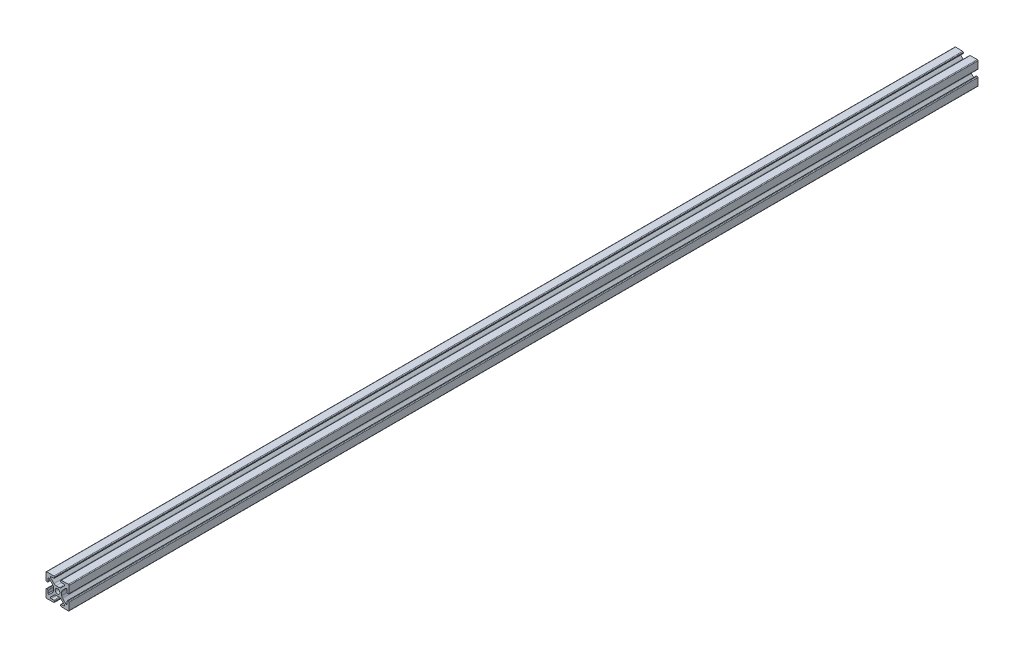
SolidWorks part; units mm, degrees
material "6061 Alloy"
ref_plane "Front Plane" through (0, 0, 0) normal (0, 0, 1) x (1, 0, 0)
ref_plane "Top Plane" through (0, 0, 0) normal (0, 1, 0) x (1, 0, 0)
ref_plane "Right Plane" through (0, 0, 0) normal (1, 0, 0) x (0, 0, -1)
sketch "Sketch1" plane through (0, 0, 0) normal (0, 0, 1) x (-1, 0, 0)
  line L72 (12.7, -11.928) -> (12.5979, -4.1277)
  line L73 (11.836, -3.3757) -> (11.2116, -3.3757)
  line L74 (10.4496, -4.1377) -> (10.4496, -7.0114)
  line L75 (9.1488, -7.5503) -> (5.5122, -3.9136)
  line L76 (4.5822, -1.6588) -> (4.5822, 1.6588)
  line L77 (5.5122, 3.9136) -> (9.1488, 7.5503)
  line L78 (10.4496, 7.0114) -> (10.4496, 4.1377)
  line L79 (11.2116, 3.3757) -> (11.836, 3.3757)
  line L80 (12.5979, 4.1277) -> (12.7, 11.928)
  line L81 (11.928, 12.7) -> (4.1277, 12.5979)
  line L82 (3.3757, 11.836) -> (3.3757, 11.2116)
  line L83 (4.1377, 10.4496) -> (7.0114, 10.4496)
  line L84 (7.5502, 9.1487) -> (3.9135, 5.5121)
  line L85 (1.6587, 4.5822) -> (-1.6686, 4.5822)
  line L86 (-3.9137, 5.5121) -> (-7.5503, 9.1487)
  line L87 (-7.0115, 10.4496) -> (-4.1377, 10.4496)
  line L88 (-3.3757, 11.2116) -> (-3.3757, 11.8359)
  line L89 (-4.1278, 12.5978) -> (-11.9281, 12.6999)
  line L90 (-12.7, 11.928) -> (-12.5979, 4.1277)
  line L91 (-11.836, 3.3757) -> (-11.2116, 3.3757)
  line L92 (-10.4496, 4.1377) -> (-10.4496, 7.0114)
  line L93 (-9.1488, 7.5503) -> (-5.5122, 3.9136)
  line L94 (-4.5822, 1.6588) -> (-4.5822, -1.6588)
  line L95 (-5.5122, -3.9136) -> (-9.1488, -7.5503)
  line L96 (-10.4496, -7.0114) -> (-10.4496, -4.1377)
  line L97 (-11.2116, -3.3757) -> (-11.836, -3.3757)
  line L98 (-12.5979, -4.1277) -> (-12.7, -11.928)
  line L99 (-11.928, -12.7) -> (-4.1277, -12.5979)
  line L100 (-3.3757, -11.836) -> (-3.3757, -11.2116)
  line L101 (-4.1377, -10.4496) -> (-7.0114, -10.4496)
  line L102 (-7.5503, -9.1488) -> (-3.9136, -5.5122)
  line L103 (-1.6685, -4.5822) -> (1.6588, -4.5822)
  line L104 (3.9136, -5.5122) -> (7.5503, -9.1488)
  line L105 (7.0114, -10.4496) -> (4.1377, -10.4496)
  line L106 (3.3757, -11.2116) -> (3.3757, -11.836)
  line L107 (4.1277, -12.5979) -> (11.928, -12.7)
  circle A1 centre (0, 0) radius 2.5527
  arc A72 (11.928, -12.7) -> (12.7, -11.928) centre (11.9381, -11.9381) ccw
  arc A73 (12.5979, -4.1277) -> (11.836, -3.3757) centre (11.836, -4.1377) ccw
  arc A74 (11.2116, -3.3757) -> (10.4496, -4.1377) centre (11.2116, -4.1377) ccw
  arc A75 (9.1488, -7.5503) -> (10.4496, -7.0114) centre (9.6876, -7.0114) ccw
  arc A76 (4.5822, -1.6588) -> (5.5122, -3.9136) centre (7.7809, -1.6588) ccw
  arc A77 (5.5122, 3.9136) -> (4.5822, 1.6588) centre (7.7809, 1.6588) ccw
  arc A78 (10.4496, 7.0114) -> (9.1488, 7.5503) centre (9.6876, 7.0114) ccw
  arc A79 (10.4496, 4.1377) -> (11.2116, 3.3757) centre (11.2116, 4.1377) ccw
  arc A80 (11.836, 3.3757) -> (12.5979, 4.1277) centre (11.836, 4.1377) ccw
  arc A81 (12.7, 11.928) -> (11.928, 12.7) centre (11.9381, 11.9381) ccw
  arc A82 (4.1277, 12.5979) -> (3.3757, 11.836) centre (4.1377, 11.836) ccw
  arc A83 (3.3757, 11.2116) -> (4.1377, 10.4496) centre (4.1377, 11.2116) ccw
  arc A84 (7.5502, 9.1487) -> (7.0114, 10.4496) centre (7.0114, 9.6876) ccw
  arc A85 (1.6587, 4.5822) -> (3.9135, 5.5121) centre (1.6587, 7.7808) ccw
  arc A86 (-3.9137, 5.5121) -> (-1.6686, 4.5822) centre (-1.6686, 7.7572) ccw
  arc A87 (-7.0115, 10.4496) -> (-7.5503, 9.1487) centre (-7.0115, 9.6876) ccw
  arc A88 (-4.1377, 10.4496) -> (-3.3757, 11.2116) centre (-4.1377, 11.2116) ccw
  arc A89 (-3.3757, 11.8359) -> (-4.1278, 12.5978) centre (-4.1377, 11.8359) ccw
  arc A90 (-11.9281, 12.6999) -> (-12.7, 11.928) centre (-11.9381, 11.938) ccw
  arc A91 (-12.5979, 4.1277) -> (-11.836, 3.3757) centre (-11.836, 4.1377) ccw
  arc A92 (-11.2116, 3.3757) -> (-10.4496, 4.1377) centre (-11.2116, 4.1377) ccw
  arc A93 (-9.1488, 7.5503) -> (-10.4496, 7.0114) centre (-9.6876, 7.0114) ccw
  arc A94 (-4.5822, 1.6588) -> (-5.5122, 3.9136) centre (-7.7809, 1.6588) ccw
  arc A95 (-5.5122, -3.9136) -> (-4.5822, -1.6588) centre (-7.7809, -1.6588) ccw
  arc A96 (-10.4496, -7.0114) -> (-9.1488, -7.5503) centre (-9.6876, -7.0114) ccw
  arc A97 (-10.4496, -4.1377) -> (-11.2116, -3.3757) centre (-11.2116, -4.1377) ccw
  arc A98 (-11.836, -3.3757) -> (-12.5979, -4.1277) centre (-11.836, -4.1377) ccw
  arc A99 (-12.7, -11.928) -> (-11.928, -12.7) centre (-11.9381, -11.9381) ccw
  arc A100 (-4.1277, -12.5979) -> (-3.3757, -11.836) centre (-4.1377, -11.836) ccw
  arc A101 (-3.3757, -11.2116) -> (-4.1377, -10.4496) centre (-4.1377, -11.2116) ccw
  arc A102 (-7.5503, -9.1488) -> (-7.0114, -10.4496) centre (-7.0114, -9.6876) ccw
  arc A103 (-1.6685, -4.5822) -> (-3.9136, -5.5122) centre (-1.6685, -7.7572) ccw
  arc A104 (3.9136, -5.5122) -> (1.6588, -4.5822) centre (1.6588, -7.7809) ccw
  arc A105 (7.0114, -10.4496) -> (7.5503, -9.1488) centre (7.0114, -9.6876) ccw
  arc A106 (4.1377, -10.4496) -> (3.3757, -11.2116) centre (4.1377, -11.2116) ccw
  arc A107 (3.3757, -11.836) -> (4.1277, -12.5979) centre (4.1377, -11.836) ccw
  dimension "D1" = 5.1054
  dimension "D6" = 0.762
  dimension "D2" = 25.4
  dimension "D3" = 25.4
  dimension "D4" = 12.7
  dimension "D5" = 12.7
extrude "Boss-Extrude1" add sketch "Sketch1" along normal blind 1000
